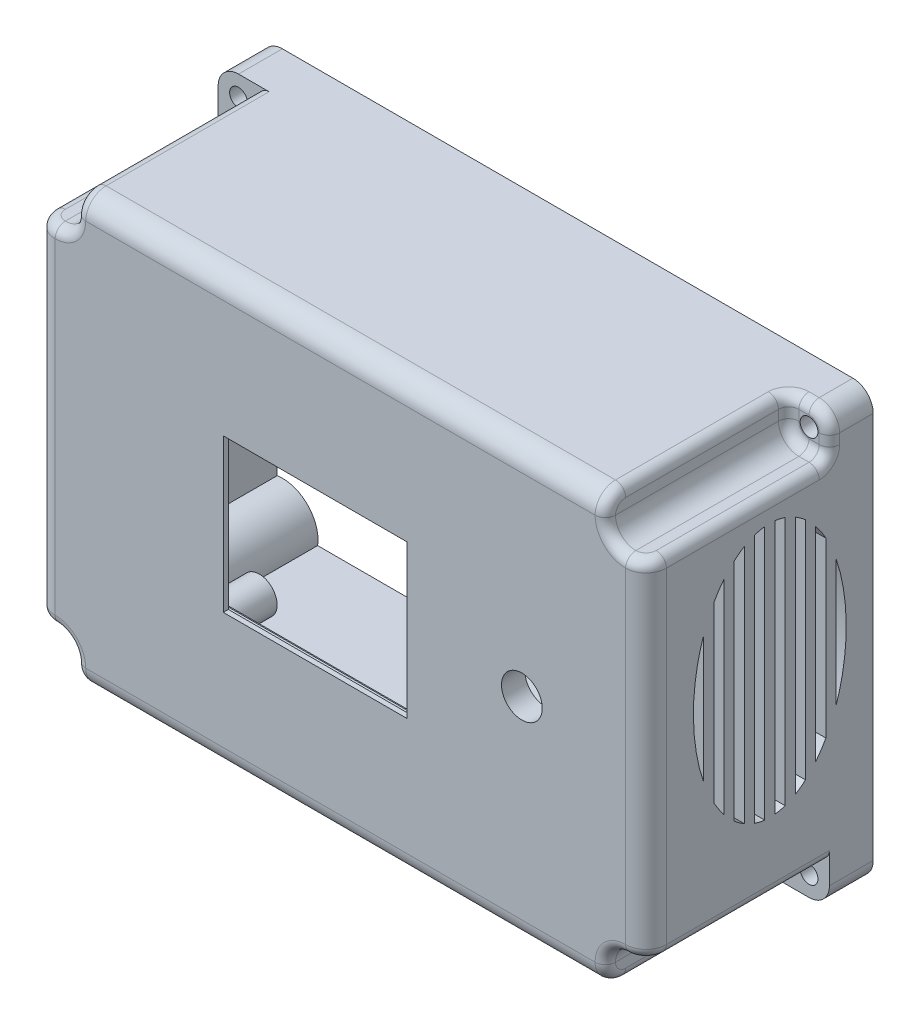
SolidWorks part; units mm, degrees
ref_plane "Front Plane" through (0, 0, 0) normal (0, 0, 1) x (1, 0, 0)
ref_plane "Top Plane" through (0, 0, 0) normal (0, 1, 0) x (1, 0, 0)
ref_plane "Right Plane" through (0, 0, 0) normal (1, 0, 0) x (0, 0, -1)
sketch "Sketch1" plane through (0, 0, 0) normal (0, 0, 1) x (1, 0, 0)
  line L1 (-22.81, -17.01) -> (22.81, -17.01)
  line L2 (-22.81, -17.01) -> (-22.81, 17.01)
  line L3 (-22.81, 17.01) -> (22.81, 17.01)
  line L4 (22.81, -17.01) -> (22.81, 17.01)
  line L5 (-22.81, -17.01) -> (22.81, 17.01) construction
  line L6 (-22.81, 17.01) -> (22.81, -17.01) construction
  line L7 (-52.81, 42.01) -> (67.19, 42.01)
  line L8 (-52.81, 42.01) -> (-52.81, -41.99)
  line L9 (-52.81, -41.99) -> (67.19, -41.99)
  line L10 (67.19, 42.01) -> (67.19, -41.99)
  circle A0 centre (42.81, 0) radius 4
  point P0 (0, 0)
  dimension "D7" = 20
  dimension "D8" = 8
  dimension "D1" = 45.62
  dimension "D2" = 34.02
  dimension "D3" = 120
  dimension "D4" = 84
  dimension "D5" = 30
  dimension "D6" = 25
extrude "Boss-Extrude1" add sketch "Sketch1" along normal blind 2.4
sketch "Sketch2" plane through (0, 0, 2.4) normal (0, 0, 1) x (1, 0, 0)
  line L0 (22.81, 17.01) -> (-22.81, 17.01) construction
  line L1 (-15.81, 15.01) -> (20.31, 15.01)
  line L2 (-15.81, 15.01) -> (-15.81, -15.01)
  line L3 (-15.81, -15.01) -> (20.31, -15.01)
  line L4 (20.31, 15.01) -> (20.31, -15.01)
  line L5 (-22.81, -17.01) -> (22.81, -17.01) construction
  line L6 (-22.81, 17.01) -> (-22.81, -17.01) construction
  line L7 (22.81, -17.01) -> (22.81, 17.01) construction
  line L9 (-52.81, 42.01) -> (67.19, 42.01)
  line L10 (-52.81, 42.01) -> (-52.81, -41.99)
  line L11 (-52.81, -41.99) -> (67.19, -41.99)
  line L12 (67.19, 42.01) -> (67.19, -41.99)
  circle A0 centre (42.81, 0) radius 4
  dimension "D1" = 2
  dimension "D2" = 2
  dimension "D3" = 7
  dimension "D4" = 2.5
extrude "Boss-Extrude2" add sketch "Sketch2" along normal blind 1
sketch "Sketch3" plane through (0, 0, 0) normal (0, 0, -1) x (-1, 0, 0)
  line L0 (22.81, 17.01) -> (22.81, -17.01) construction
  line L1 (-67.19, 42.01) -> (52.81, 42.01)
  line L2 (-67.19, 42.01) -> (-67.19, -41.99)
  line L3 (-67.19, -41.99) -> (52.81, -41.99)
  line L4 (52.81, 42.01) -> (52.81, -41.99)
  line L5 (-27.81, 18.01) -> (27.81, 18.01)
  line L6 (-27.81, 18.01) -> (-27.81, -18.01)
  line L7 (-27.81, -18.01) -> (27.81, -18.01)
  line L8 (27.81, 18.01) -> (27.81, -18.01)
  line L9 (-22.81, -17.01) -> (-22.81, 17.01) construction
  line L10 (-22.81, 17.01) -> (22.81, 17.01) construction
  line L11 (22.81, -17.01) -> (-22.81, -17.01) construction
  circle A0 centre (-42.81, 0) radius 4
  dimension "D1" = 5
  dimension "D2" = 5
  dimension "D3" = 1
  dimension "D4" = 1
extrude "Boss-Extrude3" add sketch "Sketch3" along normal blind 1.2
sketch "Sketch4" plane through (0, 0, 0) normal (0, 0, -1) x (-1, 0, 0)
  line L0 (-27.81, 18.01) -> (-27.81, -18.01) construction
  line L1 (-24.81, -12.01) -> (-27.81, -12.01)
  line L2 (-24.81, -12.01) -> (-24.81, 12.01)
  line L3 (-24.81, 12.01) -> (-27.81, 12.01)
  line L4 (-27.81, -12.01) -> (-27.81, 12.01)
  line L5 (-27.81, -18.01) -> (27.81, -18.01) construction
  line L6 (27.81, 18.01) -> (-27.81, 18.01) construction
  dimension "D1" = 3
  dimension "D2" = 6
  dimension "D3" = 6
extrude "Cut-Extrude1" cut sketch "Sketch4" against normal blind 2.5
sketch "Sketch5" plane through (0, 0, 0) normal (0, 0, -1) x (-1, 0, 0)
  line L0 (27.81, 18.01) -> (-27.81, 18.01) construction
  line L1 (-27.81, 18.01) -> (-27.81, 12.01) construction
  circle A0 centre (-25.81, 16.01) radius 1.2
  circle A1 centre (25.5751, 16.01) radius 1.2
  circle A2 centre (25.5751, -16.3798) radius 1.2
  circle A3 centre (-25.81, -16.3798) radius 1.2
  dimension "D1" = 2
  dimension "D2" = 2
  dimension "D3" = 2.4
extrude "Cut-Extrude2" cut sketch "Sketch5" against normal blind 2
sketch "Sketch6" plane through (0, 0, -1.2) normal (0, 0, -1) x (-1, 0, 0)
  line L1 (-56.41, 12) -> (-49.41, 12)
  line L2 (-56.41, 12) -> (-56.41, -8)
  line L3 (-56.41, -8) -> (-49.41, -8)
  line L4 (-49.41, 12) -> (-49.41, -8)
  circle A0 centre (-51.41, -5) radius 1.75
  circle A1 centre (-51.41, 9) radius 1.75
  circle A2 centre (-42.81, 0) radius 4 construction
  dimension "D1" = 8.6
  dimension "D2" = 8.6
  dimension "D3" = 5
  dimension "D4" = 9
  dimension "D5" = 3.5
  dimension "D6" = 3.5
  dimension "D7" = 3
  dimension "D8" = 3
  dimension "D9" = 5
  dimension "D10" = 2
extrude "Boss-Extrude4" add sketch "Sketch6" along normal blind 4.5
sketch "Sketch8" plane through (0, 0, -1.2) normal (0, 0, -1) x (-1, 0, 0)
  line L0 (52.81, 42.01) -> (-67.19, 42.01) construction
  circle A0 centre (27.3361, 25.01) radius 1.75
  circle A1 centre (27.3361, 25.01) radius 3.5
  circle A2 centre (-36.1639, 25.01) radius 1.75
  circle A3 centre (-36.1639, 25.01) radius 3.5
  circle A4 centre (27.3361, -27.06) radius 1.75
  circle A5 centre (-36.1639, -27.06) radius 1.75
  circle A6 centre (-36.1639, -27.06) radius 3.5
  circle A7 centre (27.3361, -27.06) radius 3.5
  dimension "D1" = 17
  dimension "D2" = 3.5
  dimension "D3" = 7
  dimension "D4" = 3.5
  dimension "D5" = 63.5
  dimension "D6" = 7
  dimension "D7" = 52.07
  dimension "D8" = 3.5
  dimension "D9" = 3.5
extrude "Boss-Extrude6" add sketch "Sketch8" along normal blind 14
sketch "Sketch9" plane through (0, 0, -1.2) normal (0, 0, -1) x (-1, 0, 0)
  line L1 (-67.19, 42.01) -> (52.81, 42.01)
  line L2 (-67.19, 42.01) -> (-67.19, -41.99)
  line L3 (-67.19, -41.99) -> (52.81, -41.99)
  line L4 (52.81, 42.01) -> (52.81, -41.99)
  line L5 (-64.19, 39.01) -> (49.81, 39.01)
  line L6 (-64.19, 39.01) -> (-64.19, -38.99)
  line L7 (-64.19, -38.99) -> (49.81, -38.99)
  line L8 (49.81, 39.01) -> (49.81, -38.99)
  dimension "D1" = 3
  dimension "D2" = 3
  dimension "D3" = 3
  dimension "D4" = 3
extrude "Boss-Extrude7" add sketch "Sketch9" along normal blind 40
fillet "Fillet1" radius 4 8 edges at (67.19, 42.01, -18.9) (67.19, -41.99, -18.9) (-52.81, 42.01, -18.9) (7.19, 42.01, 3.4) (-52.81, 0.01, 3.4) (7.19, -41.99, 3.4) (67.19, 0.01, 3.4) (-52.81, -41.99, -18.9)
sketch "Sketch10" plane through (0, 0, -41.2) normal (0, 0, -1) x (-1, 0, 0)
  line L0 (48.81, 42.01) -> (-63.19, 42.01) construction
  line L1 (-67.19, 38.01) -> (-67.19, -37.99) construction
  circle A0 centre (-63.19, 38.01) radius 4
  circle A2 centre (48.81, -37.99) radius 4
  circle A3 centre (48.81, 38.01) radius 4
  circle A4 centre (-63.19, -37.99) radius 4
  dimension "D1" = 4
  dimension "D2" = 4
  dimension "D3" = 8
extrude "Boss-Extrude8" add sketch "Sketch10" against normal up to surface (40 mm away) up to face at (7.19, 0.01, -1.2)
sketch "Sketch11" plane through (0, 0, -41.2) normal (0, 0, -1) x (-1, 0, 0)
  circle A0 centre (-63.19, 38.01) radius 1.75
  circle A1 centre (48.81, 38.01) radius 1.75
  circle A2 centre (48.81, -37.99) radius 1.75
  circle A3 centre (-63.19, -37.99) radius 1.75
  dimension "D1" = 3.5
extrude "Cut-Extrude3" cut sketch "Sketch11" against normal through all
sketch "Sketch12" plane through (0, 0, -41.2) normal (0, 0, -1) x (-1, 0, 0)
  line L0 (41.8818, 39.01) -> (44.937, 39.01)
  line L1 (-59.317, 39.01) -> (-56.2618, 39.01)
  line L2 (-64.19, 34.137) -> (-64.19, 31.0818)
  line L3 (-59.317, -38.99) -> (-56.2618, -38.99)
  line L4 (49.81, 34.137) -> (49.81, 31.0818)
  line L5 (-64.19, -31.0618) -> (-64.19, -34.117)
  line L6 (41.8818, -38.99) -> (44.937, -38.99)
  line L7 (49.81, -31.0618) -> (49.81, -34.117)
  arc A0 (-64.19, 34.137) -> (-59.317, 39.01) centre (-63.19, 38.01) ccw
  arc A1 (44.937, 39.01) -> (49.81, 34.137) centre (48.81, 38.01) ccw
  arc A2 (49.81, -34.117) -> (44.937, -38.99) centre (48.81, -37.99) ccw
  arc A3 (-59.317, -38.99) -> (-64.19, -34.117) centre (-63.19, -37.99) ccw
  arc A4 (-56.2618, -38.99) -> (-64.19, -31.0618) centre (-63.19, -37.99) ccw
  arc A5 (-64.19, 31.0818) -> (-56.2618, 39.01) centre (-63.19, 38.01) ccw
  arc A6 (41.8818, 39.01) -> (49.81, 31.0818) centre (48.81, 38.01) ccw
  arc A7 (49.81, -31.0618) -> (41.8818, -38.99) centre (48.81, -37.99) ccw
  dimension "D1" = 3
extrude "Boss-Extrude9" add sketch "Sketch12" against normal up to surface (40 mm away) up to face at (7.19, 0.01, -1.2)
sketch "Sketch13" plane through (0, 0, 3.4) normal (0, 0, 1) x (1, 0, 0)
  line L0 (-52.81, 0.01) -> (67.19, 0.01) construction
  line L2 (-48.81, -33.99) -> (-52.81, -33.99)
  line L3 (-44.81, -37.99) -> (-44.81, -41.99)
  line L4 (-44.81, -41.99) -> (-48.81, -41.99)
  line L5 (-52.81, -33.99) -> (-52.81, -37.99)
  line L6 (-52.81, -37.99) -> (-52.81, 38.01) construction
  line L7 (67.19, 38.01) -> (67.19, -37.99) construction
  line L8 (7.19, 0.01) -> (7.19, -44.0511) construction
  line L9 (63.19, -33.99) -> (67.19, -33.99)
  line L10 (67.19, -33.99) -> (67.19, -37.99)
  line L11 (59.19, -41.99) -> (63.19, -41.99)
  line L12 (59.19, -37.99) -> (59.19, -41.99)
  line L13 (59.19, 38.01) -> (59.19, 42.01)
  line L14 (59.19, 42.01) -> (63.19, 42.01)
  line L15 (67.19, 34.01) -> (67.19, 38.01)
  line L16 (63.19, 34.01) -> (67.19, 34.01)
  line L17 (-48.81, 34.01) -> (-52.81, 34.01)
  line L18 (-52.81, 34.01) -> (-52.81, 38.01)
  line L19 (-44.81, 42.01) -> (-48.81, 42.01)
  line L20 (-44.81, 38.01) -> (-44.81, 42.01)
  arc A3 (-44.81, -37.99) -> (-48.81, -33.99) centre (-48.81, -37.99) ccw
  arc A4 (-52.81, -37.99) -> (-48.81, -41.99) centre (-48.81, -37.99) ccw
  arc A5 (59.19, -37.99) -> (63.19, -33.99) centre (63.19, -37.99) cw
  arc A6 (67.19, -37.99) -> (63.19, -41.99) centre (63.19, -37.99) cw
  arc A7 (67.19, 38.01) -> (63.19, 42.01) centre (63.19, 38.01) ccw
  arc A8 (59.19, 38.01) -> (63.19, 34.01) centre (63.19, 38.01) ccw
  arc A9 (-44.81, 38.01) -> (-48.81, 34.01) centre (-48.81, 38.01) cw
  arc A10 (-52.81, 38.01) -> (-48.81, 42.01) centre (-48.81, 38.01) cw
extrude "Cut-Extrude4" cut sketch "Sketch13" against normal blind 36
fillet "Fillet3" radius 2 26 edges at (66.0184, 40.8384, -32.6) (67.19, 36.01, -32.6) (61.19, 42.01, -32.6) (65.19, 34.01, -32.6) (60.3616, 35.1816, -32.6) (67.19, 34.01, -16.6) (66.0184, 34.01, 2.2284) (60.3616, 35.1816, 3.4) (67.19, -33.99, -16.6) (66.0184, -33.99, 2.2284) (60.3616, -35.1616, 3.4) (59.19, -40.8184, 2.2284) (-44.81, -41.99, -16.6) (-44.81, -40.8184, 2.2284) (-45.9816, -35.1616, 3.4) (-51.6384, -33.99, 2.2284) (-44.81, 42.01, -16.6) (-44.81, 40.8384, 2.2284) (-45.9816, 35.1816, 3.4) (-51.6384, 34.01, 2.2284) (59.19, 42.01, -16.6) (59.19, 40.01, -32.6) (59.19, 40.8384, 2.2284) (59.19, -41.99, -16.6) (-52.81, -33.99, -16.6) (-52.81, 34.01, -16.6)
sketch "Sketch14" plane through (-49.81, 0, 0) normal (1, 0, 0) x (0, 0, -1)
  line L0 (1.2, -31.0618) -> (41.2, -31.0618) construction
  line L1 (14.0443, -31.0618) -> (29.5443, -31.0618)
  line L2 (14.0443, -31.0618) -> (14.0443, -23.0618)
  line L3 (14.0443, -23.0618) -> (29.5443, -23.0618)
  line L4 (29.5443, -31.0618) -> (29.5443, -23.0618)
  dimension "D1" = 15.5
  dimension "D2" = 8
extrude "Cut-Extrude5" cut sketch "Sketch14" against normal through all
sketch "Sketch15" plane through (-52.81, 0, 0) normal (-1, 0, 0) x (0, 0, 1)
  line L0 (-16.7443, -31.0618) -> (-14.0443, -31.0618)
  line L1 (-14.0443, -31.0618) -> (-29.5443, -31.0618) construction
  line L2 (-14.0443, -31.0618) -> (-14.0443, -28.2618)
  line L3 (-14.0443, -23.0618) -> (-14.0443, -31.0618) construction
  line L4 (-16.7443, -31.0618) -> (-14.0443, -28.2618)
  line L5 (-14.0443, -27.0618) -> (-29.5443, -27.0618) construction
  line L6 (-29.5443, -31.0618) -> (-29.5443, -23.0618) construction
  line L7 (-16.7443, -23.0618) -> (-14.0443, -23.0618)
  line L8 (-14.0443, -23.0618) -> (-14.0443, -25.8618)
  line L9 (-16.7443, -23.0618) -> (-14.0443, -25.8618)
  dimension "D1" = 2.8
  dimension "D2" = 2.7
extrude "Boss-Extrude10" add sketch "Sketch15" against normal up to surface (3 mm away) up to face at (-49.81, -13.5259, -21.4972)
sketch "Sketch16" plane through (-52.81, 0, 0) normal (-1, 0, 0) x (0, 0, 1)
  line L0 (-41.2, -37.99) -> (-41.2, 38.01) construction
  line L1 (-0.6, -31.99) -> (-0.6, 32.01) construction
  line L2 (-0.6, 32.01) -> (-32.6, 32.01) construction
  line L3 (-32.6, -31.99) -> (-0.6, -31.99) construction
  line L4 (-29.5443, -23.0618) -> (-16.7443, -23.0618) construction
  line L6 (-33.9, 16.9454) -> (-33.9, -7.999)
  line L7 (-31.9, 21.4699) -> (-31.9, -12.5235)
  line L8 (-29.9, 24.4732) -> (-29.9, -15.5268)
  line L9 (-27.9, 26.584) -> (-27.9, -17.6376)
  line L10 (-25.9, 28.0434) -> (-25.9, -19.097)
  line L11 (-23.9, 28.9681) -> (-23.9, -20.0217)
  line L12 (-21.9, 29.4176) -> (-21.9, -20.4712)
  line L13 (-19.9, 29.4176) -> (-19.9, -20.4712)
  line L14 (-17.9, 28.9681) -> (-17.9, -20.0217)
  line L15 (-15.9, 28.0434) -> (-15.9, -19.097)
  line L16 (-13.9, 26.584) -> (-13.9, -17.6376)
  line L17 (-11.9, 24.4732) -> (-11.9, -15.5268)
  line L18 (-9.9, 21.4699) -> (-9.9, -12.5235)
  line L19 (-7.9, 16.9454) -> (-7.9, -7.999)
  ellipse E0 centre (-20.9, 4.4732) end of major axis (-20.9, -20.5268) minor radius 15 (-31.9, -12.5235) -> (-29.9, -15.5268) ccw
  ellipse E1 centre (-20.9, 4.4732) end of major axis (-20.9, -20.5268) minor radius 15 (-27.9, -17.6376) -> (-25.9, -19.097) ccw
  ellipse E2 centre (-20.9, 4.4732) end of major axis (-20.9, -20.5268) minor radius 15 (-23.9, -20.0217) -> (-21.9, -20.4712) ccw
  ellipse E3 centre (-20.9, 4.4732) end of major axis (-20.9, -20.5268) minor radius 15 (-19.9, -20.4712) -> (-17.9, -20.0217) ccw
  ellipse E4 centre (-20.9, 4.4732) end of major axis (-20.9, -20.5268) minor radius 15 (-15.9, -19.097) -> (-13.9, -17.6376) ccw
  ellipse E5 centre (-20.9, 4.4732) end of major axis (-20.9, -20.5268) minor radius 15 (-11.9, -15.5268) -> (-9.9, -12.5235) ccw
  ellipse E6 centre (-20.9, 4.4732) end of major axis (-20.9, -20.5268) minor radius 15 (-7.9, -7.999) -> (-7.9, 16.9454) ccw
  ellipse E7 centre (-20.9, 4.4732) end of major axis (-20.9, -20.5268) minor radius 15 (-9.9, 21.4699) -> (-11.9, 24.4732) ccw
  ellipse E8 centre (-20.9, 4.4732) end of major axis (-20.9, -20.5268) minor radius 15 (-13.9, 26.584) -> (-15.9, 28.0434) ccw
  ellipse E9 centre (-20.9, 4.4732) end of major axis (-20.9, -20.5268) minor radius 15 (-17.9, 28.9681) -> (-19.9, 29.4176) ccw
  ellipse E10 centre (-20.9, 4.4732) end of major axis (-20.9, -20.5268) minor radius 15 (-21.9, 29.4176) -> (-23.9, 28.9681) ccw
  ellipse E11 centre (-20.9, 4.4732) end of major axis (-20.9, -20.5268) minor radius 15 (-25.9, 28.0434) -> (-27.9, 26.584) ccw
  ellipse E12 centre (-20.9, 4.4732) end of major axis (-20.9, -20.5268) minor radius 15 (-29.9, 24.4732) -> (-31.9, 21.4699) ccw
  ellipse E13 centre (-20.9, 4.4732) end of major axis (-20.9, -20.5268) minor radius 15 (-33.9, 16.9454) -> (-33.9, -7.999) ccw
  dimension "D1" = 20.3
  dimension "D2" = 20.3
  dimension "D3" = 64
  dimension "D4" = 27.535
  dimension "D5" = 27.5368
  dimension "D6" = 15
  dimension "D7" = 25
extrude "Cut-Extrude6" cut sketch "Sketch16" against normal through all both and the other way through all
sketch "Sketch17" plane through (0, 0, -15.2) normal (0, 0, -1) x (-1, 0, 0)
  circle A0 centre (-36.1639, 25.01) radius 1.75
  circle A1 centre (-36.1639, 25.01) radius 3.5
  circle A2 centre (27.3361, 25.01) radius 1.75
  circle A3 centre (27.3361, 25.01) radius 3.5
extrude "Boss-Extrude11" add sketch "Sketch17" against normal up to surface (14 mm away) up to face at (7.19, 0.01, -1.2)
sketch "Sketch18" plane through (-49.81, 0, 0) normal (1, 0, 0) x (0, 0, -1)
  line L0 (29.5443, -23.0618) -> (29.5443, -31.0618)
  line L1 (29.5443, -31.0618) -> (16.7443, -31.0618)
  line L2 (16.7443, -31.0618) -> (14.0443, -28.2618)
  line L3 (14.0443, -28.2618) -> (14.0443, -25.8618)
  line L4 (14.0443, -25.8618) -> (14.0443, -23.0618)
  line L6 (29.5443, -23.0618) -> (31.9565, -23.0618)
  line L7 (11.1742, -23.0618) -> (14.0443, -23.0618)
  line L8 (11.1742, -23.0618) -> (11.1742, -32.4368)
  line L9 (11.1742, -32.4368) -> (31.9565, -32.4368)
  line L10 (31.9565, -23.0618) -> (31.9565, -32.4368)
